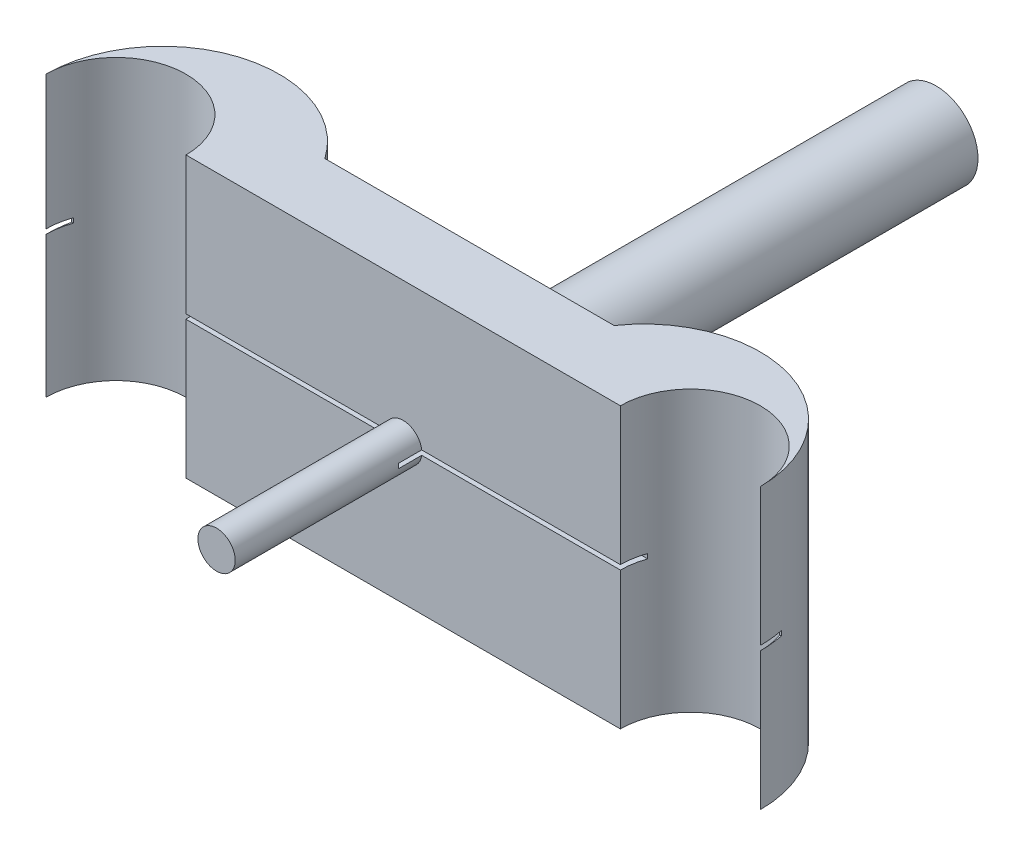
SolidWorks part; units mm, degrees
ref_plane "Front Plane" through (0, 0, 0) normal (0, 0, 1) x (1, 0, 0)
ref_plane "Top Plane" through (0, 0, 0) normal (0, 1, 0) x (1, 0, 0)
ref_plane "Right Plane" through (0, 0, 0) normal (1, 0, 0) x (0, 0, -1)
sketch "Sketch1" plane through (0, 0, 0) normal (0, 1, 0) x (1, 0, 0)
  line L0 (0, 0) -> (61.56, 0) construction
  line L2 (15.2814, 7.1093) -> (46.2786, 7.1093)
  line L3 (7.5, 0) -> (54.06, 0)
  arc A0 (7.5, 0) -> (-7.5, 0) centre (0, 0) ccw
  arc A1 (69.06, 0) -> (54.06, 0) centre (61.56, 0) ccw
  arc A2 (15.2814, 7.1093) -> (-7.5, 0) centre (5, 0) ccw
  arc A3 (69.06, 0) -> (46.2786, 7.1093) centre (56.56, 0) ccw
  dimension "D2" = 15
  dimension "D3" = 15
  dimension "D1" = 61.56
  dimension "D4" = 5
  dimension "D5" = 5
extrude "Boss-Extrude1" add sketch "Sketch1" along normal blind 30
sketch "Sketch3" plane through (0, 0, -7.1093) normal (0, 0, -1) x (-1, 0, 0)
  line L0 (-46.2786, 15) -> (-15.2814, 15) construction
  line L1 (-46.2786, 30) -> (-46.2786, 0) construction
  line L2 (-15.2814, 30) -> (-15.2814, 0) construction
  circle A0 centre (-30.78, 15) radius 4.5
  circle A1 centre (-30.78, 15) radius 2.5
  dimension "D1" = 5
  dimension "D2" = 9
extrude "Boss-Extrude3" add sketch "Sketch3" along normal blind 50
sketch "Sketch7" plane through (0, 0, 0) normal (1, 0, 0) x (0, 0, -1)
  circle A0 centre (53.0423, 15) radius 1.5
  dimension "D1" = 3
extrude "Cut-Extrude2" cut sketch "Sketch7" along normal up to surface (28.28 mm away) up to face at (28.28, 15, -57.1093)
cosmetic thread "Cosmetic Thread2" parameters "D2"=4
sketch "Sketch8" plane through (0, 0, 0) normal (0, 0, 1) x (1, 0, 0)
  line L0 (7.5, 15) -> (54.06, 15) construction
  line L1 (7.5, 30) -> (7.5, 0) construction
  line L2 (54.06, 30) -> (54.06, 0) construction
  circle A0 centre (30.78, 15) radius 2
  dimension "D1" = 4
extrude "Boss-Extrude6" add sketch "Sketch8" along normal blind 20
cosmetic thread "Cosmetic Thread1" parameters "D2"=3
sketch "Sketch9" plane through (0, 0, 0) normal (1, 0, 0) x (0, 0, -1)
  line L0 (0, 30) -> (0, 0) construction
  line L2 (-2.5, 15.632) -> (2.5, 15.632)
  line L3 (-2.5, 15.632) -> (-2.5, 15.132)
  line L4 (-2.5, 15.132) -> (2.5, 15.132)
  line L5 (2.5, 15.632) -> (2.5, 15.132)
  line L6 (-2.5, 15.632) -> (2.5, 15.132) construction
  line L7 (-2.5, 15.132) -> (2.5, 15.632) construction
  point P4 (0, 15.382)
  dimension "D1" = 0.5
  dimension "D2" = 5
extrude "Cut-Extrude14" cut sketch "Sketch9" against normal blind 15
sketch3d "3DSketch1"
  point P0 (68.621, 9.3415, -3.2835)
sketch3d "3DSketch2"
  point P0 (68.2521, 5.1107, -4.421)
ref_plane "Plane7" through (68.2521, 0, 0) normal (-1, 0, 0) x (0, 0, -1)
sketch "Sketch11" plane through (68.2521, 0, 0) normal (-1, 0, 0) x (0, 0, -1)
  line L0 (0, 0) -> (0, -30) construction
  line L2 (2.5, -14.75) -> (-2.5, -14.75)
  line L3 (2.5, -14.75) -> (2.5, -15.25)
  line L4 (2.5, -15.25) -> (-2.5, -15.25)
  line L5 (-2.5, -14.75) -> (-2.5, -15.25)
  line L6 (2.5, -14.75) -> (-2.5, -15.25) construction
  line L7 (2.5, -15.25) -> (-2.5, -14.75) construction
  point P4 (0, -15)
  dimension "D1" = 0.5
  dimension "D2" = 5
extrude "Cut-Extrude16" cut sketch "Sketch11" along normal blind 1 and the other way blind 4
fillet "Fillet1" radius 0.5 1 edges at (35.28, 15, -7.1093)
sketch "Sketch10" plane through (0, 0, 0) normal (1, 0, 0) x (0, 0, -1)
  line L0 (0, 30) -> (0, 0) construction
  line L2 (-2.5, 14.75) -> (2.5, 14.75)
  line L3 (-2.5, 14.75) -> (-2.5, 15.25)
  line L4 (-2.5, 15.25) -> (2.5, 15.25)
  line L5 (2.5, 14.75) -> (2.5, 15.25)
  line L6 (-2.5, 14.75) -> (2.5, 15.25) construction
  line L7 (-2.5, 15.25) -> (2.5, 14.75) construction
  point P2 (0, 15)
  dimension "D2" = 5
  dimension "D3" = 0.5
extrude "Cut-Extrude15" cut sketch "Sketch10" along normal offset from surface (107.7796 mm away) 75 up to face at (32.78, 15, 20) offset beyond the face yes
